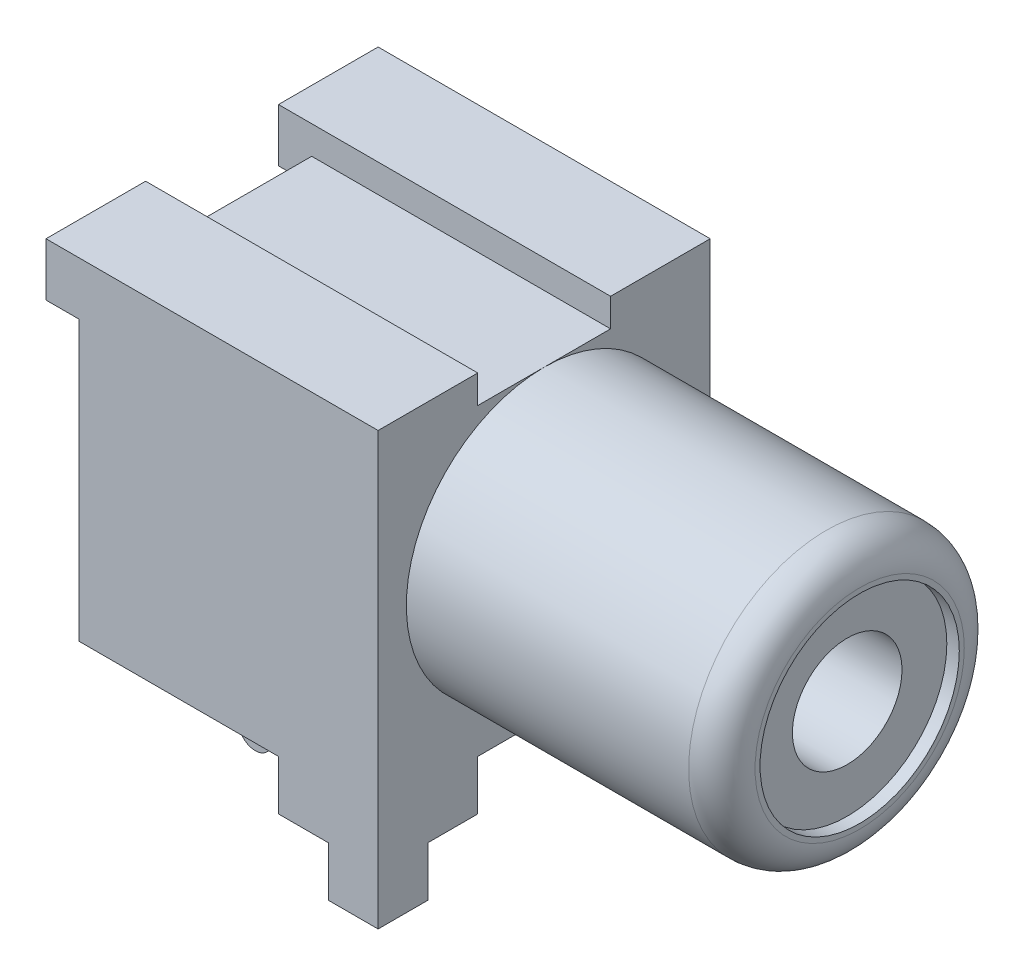
SolidWorks part; units mm, degrees
ref_plane "Plano frontal" through (0, 0, 0) normal (0, 0, 1) x (1, 0, 0)
ref_plane "Plano superior" through (0, 0, 0) normal (0, 1, 0) x (1, 0, 0)
ref_plane "Plano direito" through (0, 0, 0) normal (1, 0, 0) x (0, 0, -1)
ref_plane "Plano1" through (10, 0, 0) normal (1, 0, 0) x (0, 0, -1)
sketch "Esboço1" plane through (10, 0, 0) normal (1, 0, 0) x (0, 0, -1)
  line L0 (5, 5) -> (-5, 5)
  line L1 (-5, 5) -> (-5, -6.5)
  line L2 (-5, -6.5) -> (5, -6.5)
  line L3 (5, -6.5) -> (5, 5)
extrude "Ressalto-extrusão1" add sketch "Esboço1" against normal blind 9
sketch "Esboço2" plane through (10, 0, 0) normal (1, 0, 0) x (0, 0, -1)
  line L0 (2, 5) -> (-2, 5)
  line L1 (-2, 5) -> (-2, 4.15)
  line L2 (-2, 4.15) -> (2, 4.15)
  line L3 (2, 4.15) -> (2, 5)
extrude "Corte-extrusão1" cut sketch "Esboço2" against normal through all
sketch "Esboço3" plane through (1, 0, 0) normal (-1, 0, 0) x (0, 0, 1)
  line L0 (2, 3.4) -> (2, 5)
  line L1 (2, 5) -> (5, 5)
  line L2 (5, 5) -> (5, 3.4)
  line L3 (5, 3.4) -> (2, 3.4)
extrude "Ressalto-extrusão2" add sketch "Esboço3" along normal blind 1
sketch "Esboço4" plane through (1, 0, 0) normal (-1, 0, 0) x (0, 0, 1)
  line L0 (-5, 3.4) -> (-5, 5)
  line L1 (-5, 5) -> (-2, 5)
  line L2 (-2, 5) -> (-2, 3.4)
  line L3 (-2, 3.4) -> (-5, 3.4)
extrude "Ressalto-extrusão3" add sketch "Esboço4" along normal blind 1
sketch "Esboço5" plane through (10, 0, 0) normal (1, 0, 0) x (0, 0, -1)
  line L0 (-2, -6.5) -> (2, -6.5)
  line L1 (2, -6.5) -> (2, -5)
  line L2 (2, -5) -> (-2, -5)
  line L3 (-2, -5) -> (-2, -6.5)
extrude "Corte-extrusão2" cut sketch "Esboço5" against normal through all
sketch "Esboço6" plane through (1, 0, 0) normal (-1, 0, 0) x (0, 0, 1)
  line L0 (2, -5.5) -> (3.5, -5.5)
  line L1 (3.5, -5.5) -> (3.5, -6.5)
  line L2 (3.5, -6.5) -> (2, -6.5)
  line L3 (2, -6.5) -> (2, -5.5)
extrude "Ressalto-extrusão4" add sketch "Esboço6" along normal blind 1
sketch "Esboço7" plane through (1, 0, 0) normal (-1, 0, 0) x (0, 0, 1)
  line L0 (3.5, -5) -> (3.5, -6.5)
  line L1 (3.5, -6.5) -> (5, -6.5)
  line L2 (5, -6.5) -> (5, -5)
  line L3 (5, -5) -> (3.5, -5)
extrude "Corte-extrusão3" cut sketch "Esboço7" against normal blind 6
sketch "Esboço8" plane through (1, 0, 0) normal (-1, 0, 0) x (0, 0, 1)
  line L0 (-2, -5.5) -> (-2, -6.5)
  line L1 (-2, -6.5) -> (-3.5, -6.5)
  line L2 (-3.5, -6.5) -> (-3.5, -5.5)
  line L3 (-3.5, -5.5) -> (-2, -5.5)
extrude "Ressalto-extrusão5" add sketch "Esboço8" along normal blind 1
sketch "Esboço9" plane through (1, 0, 0) normal (-1, 0, 0) x (0, 0, 1)
  line L0 (-5, -6.5) -> (-3.5, -6.5)
  line L1 (-3.5, -6.5) -> (-3.5, -5)
  line L2 (-3.5, -5) -> (-5, -5)
  line L3 (-5, -5) -> (-5, -6.5)
extrude "Corte-extrusão4" cut sketch "Esboço9" against normal blind 6
sketch "Esboço10" plane through (0, -6.5, 0) normal (0, -1, 0) x (1, 0, 0)
  line L0 (10, 3.5) -> (8.5, 3.5)
  line L1 (8.5, 3.5) -> (8.5, 5)
  line L2 (8.5, 5) -> (10, 5)
  line L3 (10, 5) -> (10, 3.5)
extrude "Ressalto-extrusão6" add sketch "Esboço10" along normal blind 1.5
sketch "Esboço11" plane through (0, -6.5, 0) normal (0, -1, 0) x (1, 0, 0)
  line L0 (10, -5) -> (8.5, -5)
  line L1 (8.5, -5) -> (8.5, -3.5)
  line L2 (8.5, -3.5) -> (10, -3.5)
  line L3 (10, -3.5) -> (10, -5)
extrude "Ressalto-extrusão7" add sketch "Esboço11" along normal blind 1.5
sketch "Esboço12" plane through (0, 0, 0) normal (0, 0, 1) x (1, 0, 0)
  line L0 (10, 4.15) -> (10, 0)
  line L1 (10, 0) -> (19.5, 0)
  line L2 (19.5, 0) -> (19.5, 4.15)
  line L3 (19.5, 4.15) -> (10, 4.15)
  line L4 (10, 0) -> (19.5, 0) construction
revolve "Revolução1" add sketch "Esboço12" angle 360 about L4
hole_wizard "Rebaixo para parafuso de máquina de cabeça sextavada de M31" positions "Esboço14" profile "Esboço13" counterbore size "M3" standard "Ansi Metric"
sketch "Esboço14" plane through (19.5, 0, 0) normal (1, 0, 0) x (0, 0, -1)
  point P0 (0, 0)
sketch "Esboço13" plane through (19.5, 0, 0) normal (0, 1, 0) x (0, 0, -1)
  line L0 (0, 0) -> (0, 9.5)
  line L1 (0, 9.5) -> (1.65, 9.5)
  line L2 (1.65, 9.5) -> (1.65, 0.375)
  line L3 (1.65, 0.375) -> (3, 0.375)
  line L4 (3, 0.375) -> (3, 0)
  line L5 (3, 0) -> (0, 0)
  line L10 (0, 9.5) -> (-1.65, 9.5) construction
  line L11 (0, -6.35) -> (0, 107.95) construction
  dimension "Hole Dia." = 3.3
  dimension "Hole Depth" = 9.5
  dimension "C'Bore Dia." = 6
  dimension "C'Bore Depth" = 0.375
  dimension "Drill Angle" = 180
ref_plane "Plano2" through (0, 0, 0) normal (0, 0, -1) x (-1, 0, 0)
sketch "Esboço16" plane through (0, 0, 0) normal (0, 0, -1) x (-1, 0, 0)
  line L0 (-2, -5) -> (-2, -9.5)
  line L1 (-1.0193, -9.6377) -> (-0.55, -8)
  line L2 (-0.55, -8) -> (-0.8, -7.9284)
  line L3 (-0.8, -7.9284) -> (-0.8, 3.5)
  line L4 (-0.8, 3.5) -> (-1, 3.5)
  line L5 (-1, 3.5) -> (-2, -5)
  arc A0 (-2, -9.5) -> (-1.0193, -9.6377) centre (-1.5, -9.5) ccw
fillet "Filete1" radius 1 1 edges at (19.5, 0, -4.15)
extrude "Ressalto-extrusão9" add sketch "Esboço16" along normal mid plane 0.4
